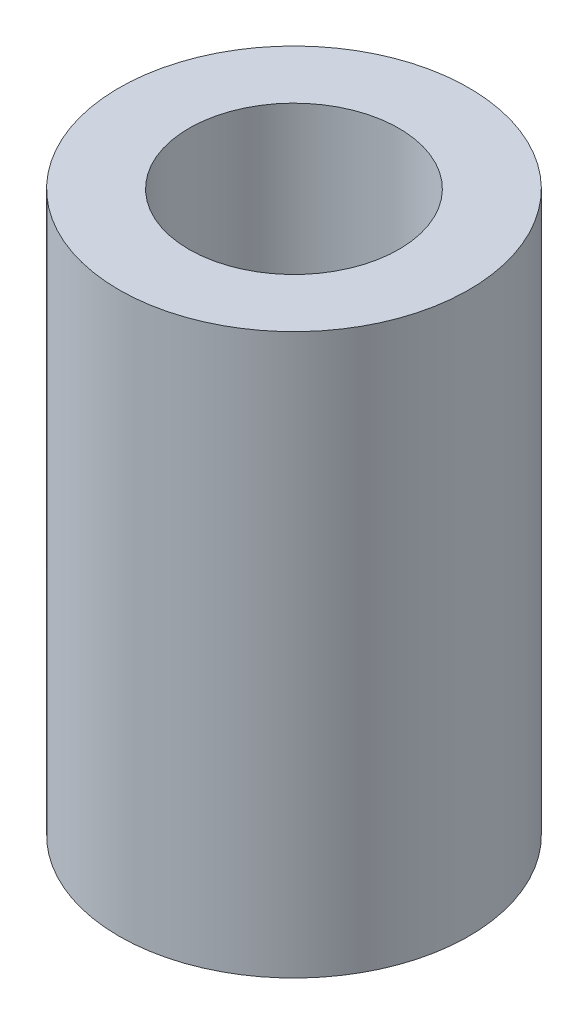
SolidWorks part; units mm, degrees
ref_plane "Plan de face" through (0, 0, 0) normal (0, 0, 1) x (1, 0, 0)
ref_plane "Plan de dessus" through (0, 0, 0) normal (0, 1, 0) x (1, 0, 0)
ref_plane "Plan de droite" through (0, 0, 0) normal (1, 0, 0) x (0, 0, -1)
sketch "Esquisse1" plane through (0, 0, 0) normal (0, 1, 0) x (1, 0, 0)
  circle A0 centre (0, 0) radius 1.25
  circle A1 centre (0, 0) radius 0.75
  dimension "D1" = 1.5
  dimension "D2" = 2.5
extrude "Extrusion1" add sketch "Esquisse1" along normal blind 4
